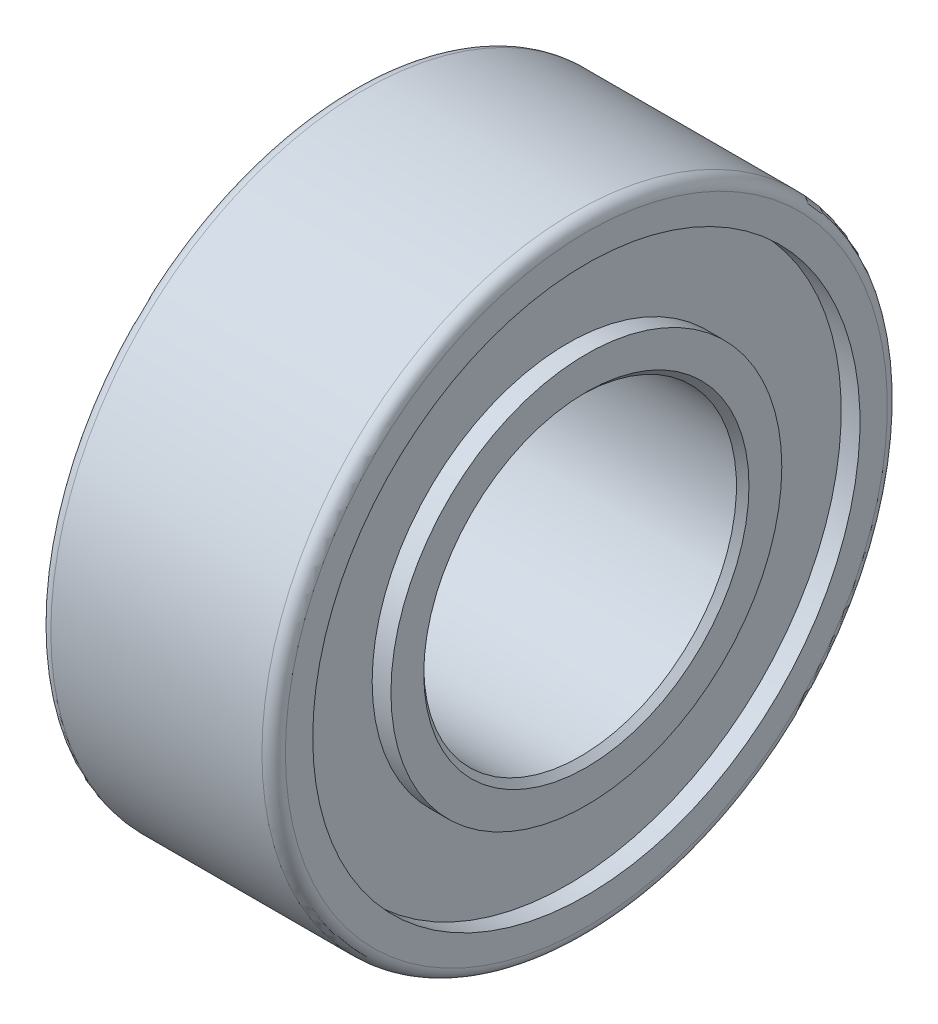
SolidWorks part; units mm, degrees
ref_plane "Front Plane" through (0, 0, 0) normal (0, 0, 1) x (1, 0, 0)
ref_plane "Top Plane" through (0, 0, 0) normal (0, 1, 0) x (1, 0, 0)
ref_plane "Right Plane" through (0, 0, 0) normal (1, 0, 0) x (0, 0, -1)
ref_plane "Plane1" through (0, 0, 0) normal (0, 0, -1) x (-1, 0, 0)
sketch "Sketch1" plane through (0, 0, 0) normal (0, 0, -1) x (-1, 0, 0)
  line L0 (-2.3813, 3.302) -> (-2.2543, 3.175)
  line L1 (-2.2543, 3.175) -> (2.2542, 3.175)
  line L2 (2.2542, 3.175) -> (2.3812, 3.302)
  line L3 (2.3812, 3.302) -> (2.3812, 3.9688)
  line L4 (2.3812, 3.9688) -> (2.0002, 3.9688)
  line L5 (2.0002, 3.9688) -> (2.0002, 5.5563)
  line L6 (2.0002, 5.5563) -> (2.3812, 5.5563)
  line L7 (2.3812, 5.5563) -> (2.3812, 6.1119)
  line L8 (2.1431, 6.35) -> (-2.1431, 6.35)
  line L9 (-2.3813, 6.1119) -> (-2.3813, 5.5563)
  line L10 (-2.3813, 5.5563) -> (-2.0003, 5.5563)
  line L11 (-2.0003, 5.5563) -> (-2.0003, 3.9688)
  line L12 (-2.0003, 3.9688) -> (-2.3813, 3.9688)
  line L13 (-2.3813, 3.9688) -> (-2.3813, 3.302)
  line L14 (-2.3825, 0) -> (2.3825, 0) construction
  arc A0 (2.3812, 6.1119) -> (2.1431, 6.35) centre (2.1431, 6.1119) ccw
  arc A1 (-2.1431, 6.35) -> (-2.3813, 6.1119) centre (-2.1431, 6.1119) ccw
revolve "Revolve1" add sketch "Sketch1" angle 360 about L14
